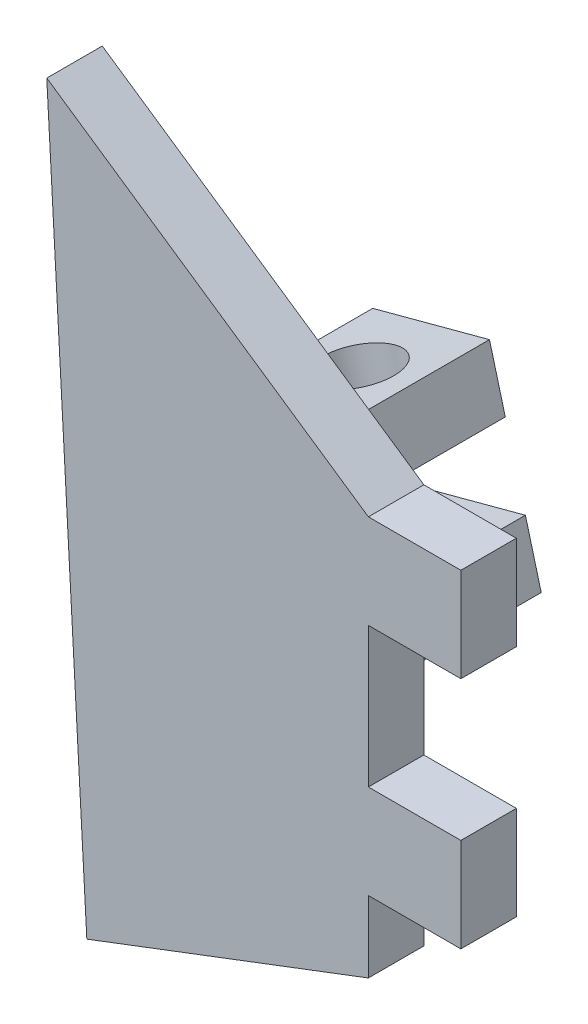
SolidWorks part; units mm, degrees
material "Acrylic (Medium-high impact)"
ref_plane "Front Plane" through (0, 0, 0) normal (0, 0, 1) x (1, 0, 0)
ref_plane "Top Plane" through (0, 0, 0) normal (0, 1, 0) x (1, 0, 0)
ref_plane "Right Plane" through (0, 0, 0) normal (1, 0, 0) x (0, 0, -1)
sketch "Sketch1" plane through (0, 0, 0) normal (0, 0, 1) x (1, 0, 0)
  line L123 (15.2195, 37.9894) -> (20.2195, 37.9894)
  line L131 (15.2195, 32.9094) -> (20.2195, 32.9094)
  line L132 (20.2195, 37.9894) -> (20.2195, 32.9094)
  line L133 (15.2195, 25.3412) -> (20.2195, 25.3412)
  line L135 (15.2195, 20.2612) -> (20.2195, 20.2612)
  line L136 (20.2195, 25.3412) -> (20.2195, 20.2612)
  line L138 (15.2195, 32.9094) -> (15.2195, 25.3412)
  line L139 (15.2195, 20.2612) -> (15.2195, 16.3994)
  line L172 (15.2195, 37.9894) -> (-2.166, 49.8405)
  line L173 (15.2195, 16.3994) -> (0, 10.6096)
  line L174 (-2.166, 49.8405) -> (0, 10.6096)
  point P12 (-9.2732, 96.4872)
  point P18 (80.0035, 87.8515)
  dimension "D19" = 5.08
  dimension "D20" = 5.08
  dimension "D27" = 5
extrude "Boss-Extrude1" add sketch "Sketch1" along normal blind 3
sketch "Sketch7" plane through (0, 0, 0) normal (0, 0, -1) x (-1, 0, 0)
  line L0 (-7.622, 31.3675) -> (-6.7666, 34.5599)
  line L1 (-6.7666, 34.5599) -> (-0.454, 32.8685)
  line L4 (-0.454, 32.8685) -> (-1.3094, 29.676)
  line L5 (-1.3094, 29.676) -> (-7.622, 31.3675)
  line L6 (-8.7091, 27.3106) -> (-2.3964, 25.6191)
  line L7 (-2.3964, 25.6191) -> (-3.2519, 22.4267)
  line L8 (-3.2519, 22.4267) -> (-9.5645, 24.1181)
  line L10 (-8.7091, 27.3106) -> (-9.5645, 24.1181)
  line L11 (-6.5268, 43.9149) -> (-6.5268, 13.0925) construction
  line L12 (-15.2195, 37.9894) -> (2.166, 49.8405) construction
  line L13 (0, 10.6096) -> (-15.2195, 16.3994) construction
  dimension "D1" = 4.2
  dimension "D2" = 105
  dimension "D3" = 6.5353
extrude "Boss-Extrude2" add sketch "Sketch7" along normal blind 12
sketch "Sketch8" plane through (-8.1867, 30.5532, 0) normal (-0.2588, 0.9659, 0) x (0.9659, 0.2588, 0)
  circle A3 centre (12.2132, 8.0444) radius 2
  dimension "D1" = 4
extrude "Cut-Extrude2" cut sketch "Sketch8" against normal through all
